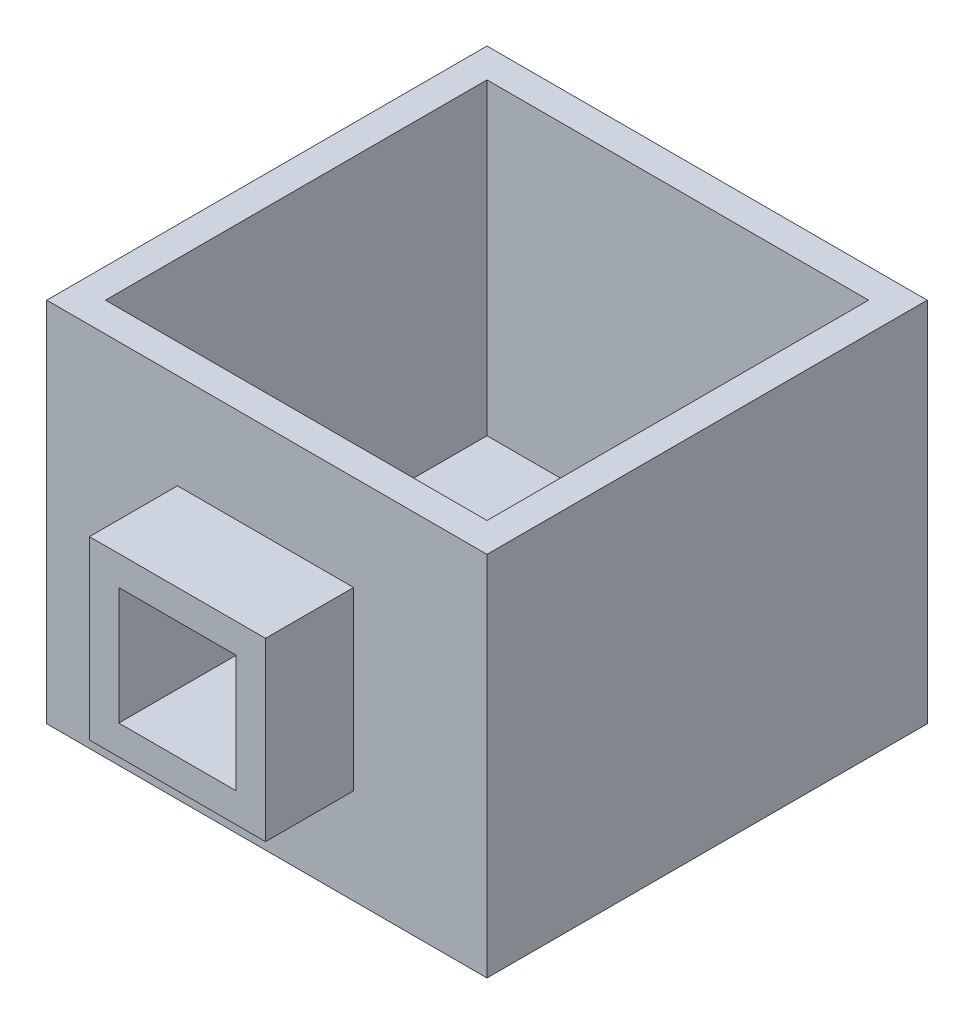
SolidWorks part; units mm, degrees
ref_plane "Front Plane" through (0, 0, 0) normal (0, 0, 1) x (1, 0, 0)
ref_plane "Top Plane" through (0, 0, 0) normal (0, 1, 0) x (1, 0, 0)
ref_plane "Right Plane" through (0, 0, 0) normal (1, 0, 0) x (0, 0, -1)
sketch "Sketch2" plane through (0, 0, 0) normal (0, 1, 0) x (1, 0, 0)
  line L1 (0, 0) -> (300, 0)
  line L2 (0, 0) -> (0, -300)
  line L3 (0, -300) -> (300, -300)
  line L4 (300, 0) -> (300, -300)
  dimension "D1" = 300
  dimension "D2" = 300
extrude "Boss-Extrude1" add sketch "Sketch2" against normal blind 250
sketch "Sketch4" plane through (0, 0, 0) normal (0, 1, 0) x (1, 0, 0)
  line L15 (0, 0) -> (0, -300) construction
  line L16 (20, -20) -> (280, -20)
  line L17 (20, -20) -> (20, -280)
  line L18 (20, -280) -> (280, -280)
  line L19 (280, -20) -> (280, -280)
  line L20 (300, -300) -> (300, 0) construction
  line L21 (300, 0) -> (0, 0) construction
  line L22 (0, -300) -> (300, -300) construction
  dimension "D1" = 20
  dimension "D2" = 20
  dimension "D3" = 20
  dimension "D4" = 20
extrude "Cut-Extrude2" cut sketch "Sketch4" against normal blind 210
sketch "Sketch6" plane through (0, 0, 300) normal (0, 0, 1) x (1, 0, 0)
  line L0 (0, -250) -> (300, -250) construction
  line L1 (89.0887, -65) -> (209.0887, -65)
  line L2 (89.0887, -65) -> (89.0887, -185)
  line L3 (89.0887, -185) -> (209.0887, -185)
  line L4 (209.0887, -65) -> (209.0887, -185)
  line L6 (109.0887, -81) -> (109.0887, -165) construction
  dimension "D1" = 120
  dimension "D2" = 120
  dimension "D3" = 65
  dimension "D4" = 20
extrude "Boss-Extrude2" add sketch "Sketch6" along normal blind 60
sketch "Sketch11" plane through (0, 0, 360) normal (0, 0, 1) x (1, 0, 0)
  line L0 (209.0887, -65) -> (89.0887, -65) construction
  line L1 (109.0887, -85) -> (189.0887, -85)
  line L2 (109.0887, -85) -> (109.0887, -165)
  line L3 (109.0887, -165) -> (189.0887, -165)
  line L4 (189.0887, -85) -> (189.0887, -165)
  line L5 (89.0887, -65) -> (89.0887, -185) construction
  dimension "D1" = 80
  dimension "D2" = 80
  dimension "D3" = 20
  dimension "D4" = 20
extrude "Cut-Extrude7" cut sketch "Sketch11" against normal up to next
